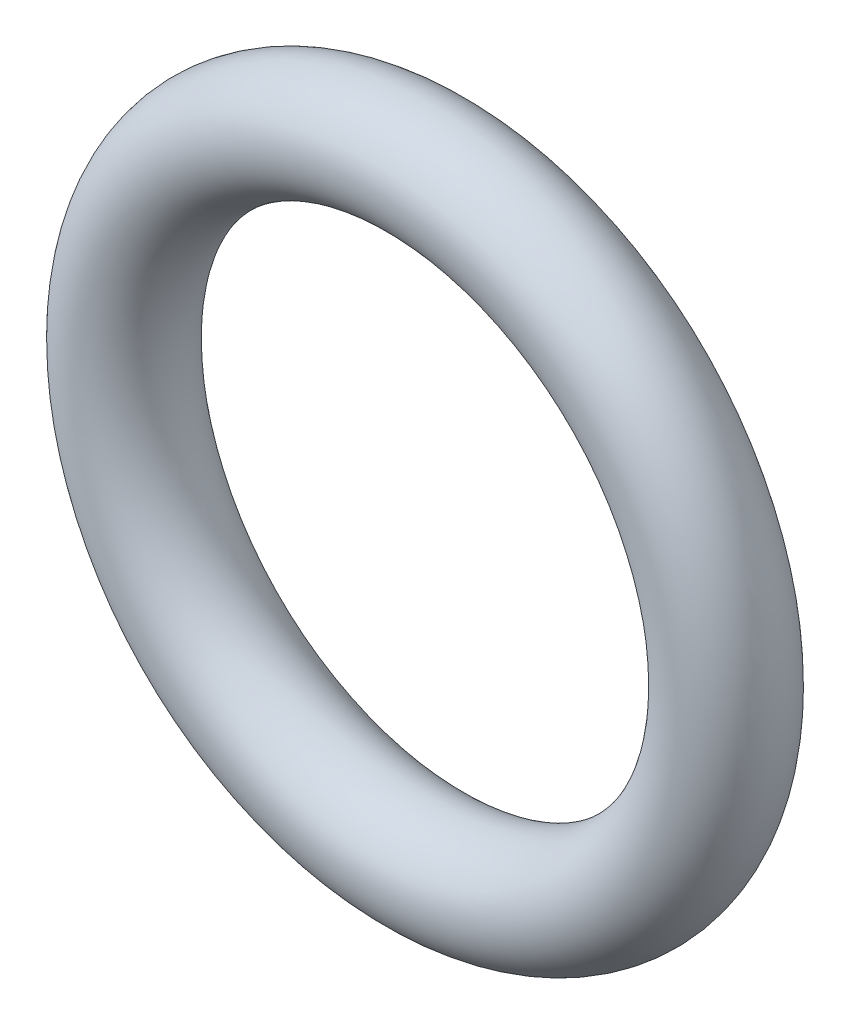
SolidWorks part; units mm, degrees
ref_plane "Front Plane" through (0, 0, 0) normal (0, 0, 1) x (1, 0, 0)
ref_plane "Top Plane" through (0, 0, 0) normal (0, 1, 0) x (1, 0, 0)
ref_plane "Right Plane" through (0, 0, 0) normal (1, 0, 0) x (0, 0, -1)
sketch "Sketch1" plane through (0, 0, 0) normal (0, 0, 1) x (1, 0, 0)
  line L0 (-3.25, 0) -> (3.25, 0) construction
  circle A0 centre (0, 0) radius 3.25
  circle A1 centre (0, 0) radius 2.25
  point P4 (2.25, 0)
  point P5 (3.25, 0)
  point P8 (0, 0)
  point P9 (0, 3.25)
  point P10 (0, -3.25)
  dimension "ID" = 4.5
  dimension "Width" = 1
  dimension "OD" = 6.5
sketch "Sketch2" plane through (0, 0, 0) normal (0, 1, 0) x (1, 0, 0)
  line L0 (-3.25, 0) -> (3.25, 0) construction
  line L1 (0, 0.5) -> (0, -0.5) construction
  circle A0 centre (2.75, 0) radius 0.5
  point P8 (0, 0)
  point P11 (2.75, 0.5)
revolve "Revolve1" add sketch "Sketch2" angle 360 about L1
sketch "Sketch3" plane through (0, 0, 0) normal (1, 0, 0) x (0, 0, -1)
  line L0 (-0.5, 0) -> (0.5, 0) construction
  line L1 (0.5, -2.75) -> (0.5, 2.75) construction
  line L3 (-0.5, 3.25) -> (0.5, 3.25) construction
  line L4 (-0.5, 3.25) -> (-0.5, -3.25) construction
  line L5 (-0.5, -3.25) -> (0.5, -3.25) construction
  line L6 (0.5, 3.25) -> (0.5, -3.25) construction
  point P2 (0, 0)
